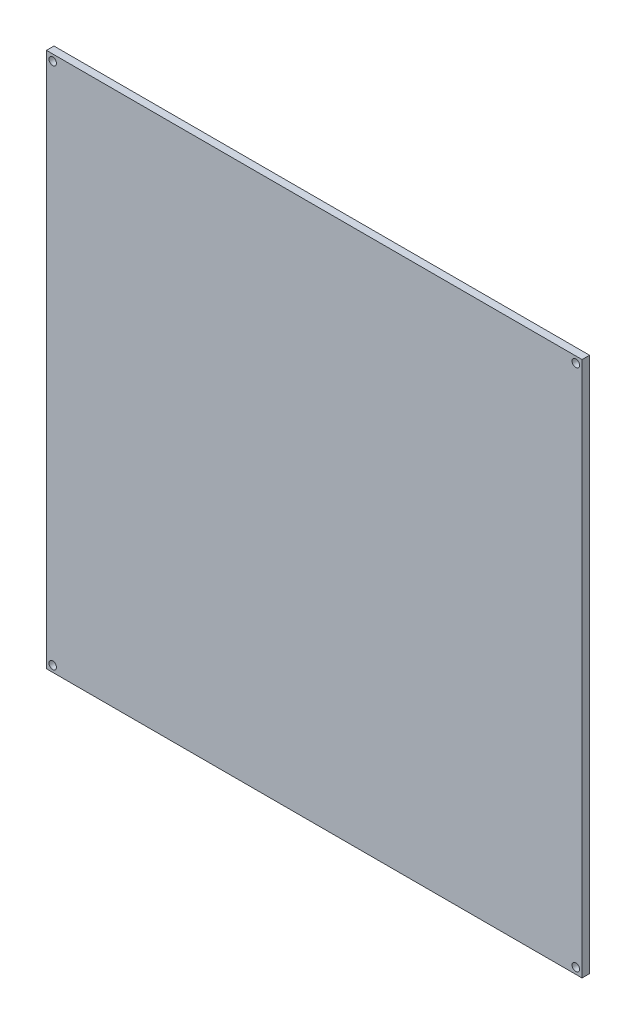
SolidWorks part; units mm, degrees
ref_plane "Plan de face" through (0, 0, 0) normal (0, 0, 1) x (1, 0, 0)
ref_plane "Plan de dessus" through (0, 0, 0) normal (0, 1, 0) x (1, 0, 0)
ref_plane "Plan de droite" through (0, 0, 0) normal (1, 0, 0) x (0, 0, -1)
sketch "Sketch1" plane through (0, 0, 0) normal (0, 0, 1) x (1, 0, 0)
  line L1 (0, 0) -> (-214, 0)
  line L2 (0, 0) -> (0, 214)
  line L3 (0, 214) -> (-214, 214)
  line L4 (-214, 0) -> (-214, 214)
  dimension "D1" = 214
  dimension "D2" = 214
extrude "Boss-Extrude1" add sketch "Sketch1" along normal blind 3
sketch "Sketch2" plane through (0, 0, 0) normal (0, 0, -1) x (-1, 0, 0)
  line L0 (0, 214) -> (214, 214) construction
  line L1 (107, 214) -> (107, 0) construction
  line L2 (214, 0) -> (0, 0) construction
  line L3 (0, 107) -> (214, 107) construction
  line L4 (0, 0) -> (0, 214) construction
  line L5 (214, 214) -> (214, 0) construction
  circle A0 centre (211.5, 211.5) radius 1.5
  circle A1 centre (2.5, 211.5) radius 1.5
  circle A2 centre (211.5, 2.5) radius 1.5
  circle A3 centre (2.5, 2.5) radius 1.5
  dimension "D1" = 3
  dimension "D2" = 2.5
  dimension "D3" = 2.5
extrude "Cut-Extrude1" cut sketch "Sketch2" against normal through all
sketch "Sketch3" plane through (0, 0, 0) normal (0, 0, -1) x (-1, 0, 0)
  line L0 (0, 107) -> (214, 107) construction
  line L1 (214, 214) -> (214, 0) construction
  line L2 (0, 0) -> (0, 214) construction
  text T0 "HOT ZONE\r\n DO NOT TOUCH" font "Century Gothic" height in points 36
extrude "Boss-Extrude2" add sketch "Sketch3" along normal blind 0.5
